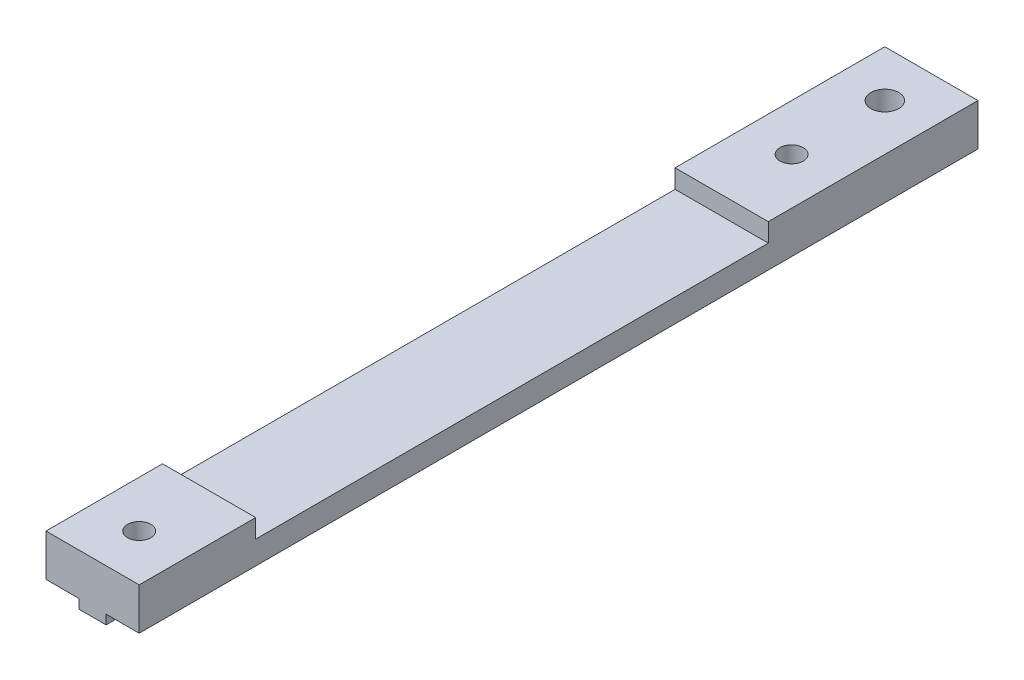
SolidWorks part; units mm, degrees
ref_plane "Front Plane" through (0, 0, 0) normal (0, 0, 1) x (1, 0, 0)
ref_plane "Top Plane" through (0, 0, 0) normal (0, 1, 0) x (1, 0, 0)
ref_plane "Right Plane" through (0, 0, 0) normal (1, 0, 0) x (0, 0, -1)
sketch "Sketch1" plane through (0, 0, 0) normal (0, 0, 1) x (1, 0, 0)
  line L0 (-5, 0) -> (5, 0)
  line L1 (5, 0) -> (5, -4.5)
  line L2 (5, -4.5) -> (1.45, -4.5)
  line L3 (1.45, -4.5) -> (1.45, -5.5)
  line L4 (1.45, -5.5) -> (-1.45, -5.5)
  line L5 (-1.45, -5.5) -> (-1.45, -4.5)
  line L6 (-1.45, -4.5) -> (-5, -4.5)
  line L7 (-5, -4.5) -> (-5, 0)
  point P9 (0, 0)
  dimension "D1" = 10
  dimension "D2" = 4.5
  dimension "D3" = 1
  dimension "D4" = 2.9
extrude "Main" add sketch "Sketch1" along normal blind 90
sketch "Sketch2" plane through (0, 0, 0) normal (0, 1, 0) x (1, 0, 0)
  line L0 (5, -90) -> (-5, -90) construction
  line L1 (5, 0) -> (-5, 0) construction
  circle A0 centre (0, -85) radius 1.25
  circle A1 centre (0, -15) radius 1.25
  circle A2 centre (0, -5) radius 1.5
  dimension "D1" = 2.5
  dimension "D4" = 3
  dimension "D2" = 5
  dimension "D3" = 70
  dimension "D5" = 5
extrude "MainHoles" cut sketch "Sketch2" against normal through all
sketch "Sketch3" plane through (0, 0, 0) normal (0, 1, 0) x (1, 0, 0)
  line L1 (-5, -90) -> (-5, 0) construction
  line L5 (5, -90) -> (5, 0) construction
  line L6 (-5, -22.5) -> (5, -22.5)
  line L7 (-5, -22.5) -> (-5, -77.5)
  line L8 (-5, -77.5) -> (5, -77.5)
  line L9 (5, -22.5) -> (5, -77.5)
  line L10 (5, -90) -> (-5, -90) construction
  dimension "D2" = 55
  dimension "D3" = 12.5
extrude "PinHoles" cut sketch "Sketch3" against normal blind 2
